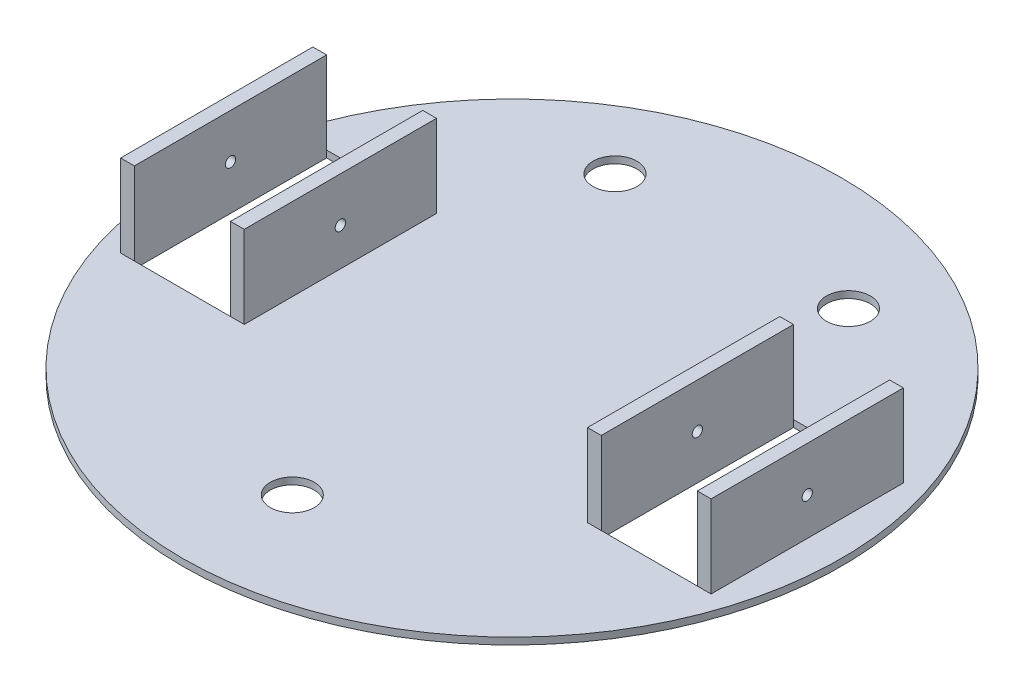
SolidWorks part; units mm, degrees
ref_plane "Front Plane" through (0, 0, 0) normal (0, 0, 1) x (1, 0, 0)
ref_plane "Top Plane" through (0, 0, 0) normal (0, 1, 0) x (1, 0, 0)
ref_plane "Right Plane" through (0, 0, 0) normal (1, 0, 0) x (0, 0, -1)
sketch "Sketch1" plane through (0, 0, 0) normal (0, 1, 0) x (1, 0, 0)
  circle A0 centre (0, 0) radius 152.4
  dimension "D1" = 304.8
extrude "Boss-Extrude1" add sketch "Sketch1" along normal blind 3.175
sketch "Sketch2" plane through (0, 3.175, 0) normal (0, 1, 0) x (1, 0, 0)
  line L0 (0, 152.4) -> (0, -152.4) construction
  line L1 (-85.725, 0) -> (85.725, 0) construction
  line L3 (-85.725, 44.45) -> (-130.175, 44.45)
  line L4 (-85.725, 44.45) -> (-85.725, -44.45)
  line L5 (-85.725, -44.45) -> (-130.175, -44.45)
  line L6 (-130.175, 44.45) -> (-130.175, -44.45)
  circle A0 centre (0, 0) radius 152.4 construction
  dimension "D1" = 171.45
  dimension "D2" = 88.9
  dimension "D3" = 44.45
extrude "Cut-Extrude1" cut sketch "Sketch2" against normal through all
sketch "Sketch3" plane through (0, 3.175, 0) normal (0, 1, 0) x (1, 0, 0)
  line L0 (-85.725, -44.45) -> (-85.725, 44.45) construction
  line L1 (-130.175, 44.45) -> (-136.525, 44.45)
  line L2 (-130.175, 44.45) -> (-130.175, -44.45)
  line L3 (-130.175, -44.45) -> (-136.525, -44.45)
  line L4 (-136.525, 44.45) -> (-136.525, -44.45)
  line L5 (-85.725, 44.45) -> (-79.375, 44.45)
  line L6 (-85.725, 44.45) -> (-85.725, -44.45)
  line L7 (-85.725, -44.45) -> (-79.375, -44.45)
  line L8 (-79.375, 44.45) -> (-79.375, -44.45)
  dimension "D1" = 6.35
  dimension "D2" = 6.35
extrude "Boss-Extrude2" add sketch "Sketch3" along normal blind 38.1
mirror "Mirror1" about plane through (0, 0, 0) normal (1, 0, 0) of "Boss-Extrude2", "Cut-Extrude1"
sketch "Sketch4" plane through (136.525, 0, 0) normal (1, 0, 0) x (0, 0, -1)
  line L0 (-152.4, 0) -> (152.4, 0) construction
  circle A0 centre (0, 20.6375) radius 2.3813
  dimension "D2" = 4.7625
  dimension "D1" = 20.6375
extrude "Cut-Extrude2" cut sketch "Sketch4" against normal through all
sketch "Sketch5" plane through (0, 3.175, 0) normal (0, 1, 0) x (1, 0, 0)
  line L0 (-203.0536, 101.6) -> (229.5216, 101.6) construction
  line L1 (0, 152.4) -> (-206.2604, 152.4) construction
  line L2 (-194.2872, 0) -> (179.1658, 0) construction
  line L3 (-159.7504, -152.4) -> (141.9723, -152.4) construction
  line L4 (0, 114.382) -> (0, -172.9748) construction
  circle A0 centre (0, -101.6) radius 10.16
  circle A1 centre (0, 0) radius 152.4 construction
  circle A2 centre (-53.975, 101.6) radius 10.16
  circle A3 centre (53.975, 101.6) radius 10.16
  dimension "D5" = 20.32
  dimension "D6" = 20.32
  dimension "D7" = 20.32
  dimension "D1" = 50.8
  dimension "D2" = 101.6
  dimension "D3" = 152.4
  dimension "D4" = 50.8
  dimension "D8" = 107.95
  dimension "D9" = 53.975
extrude "Cut-Extrude3" cut sketch "Sketch5" against normal through all
